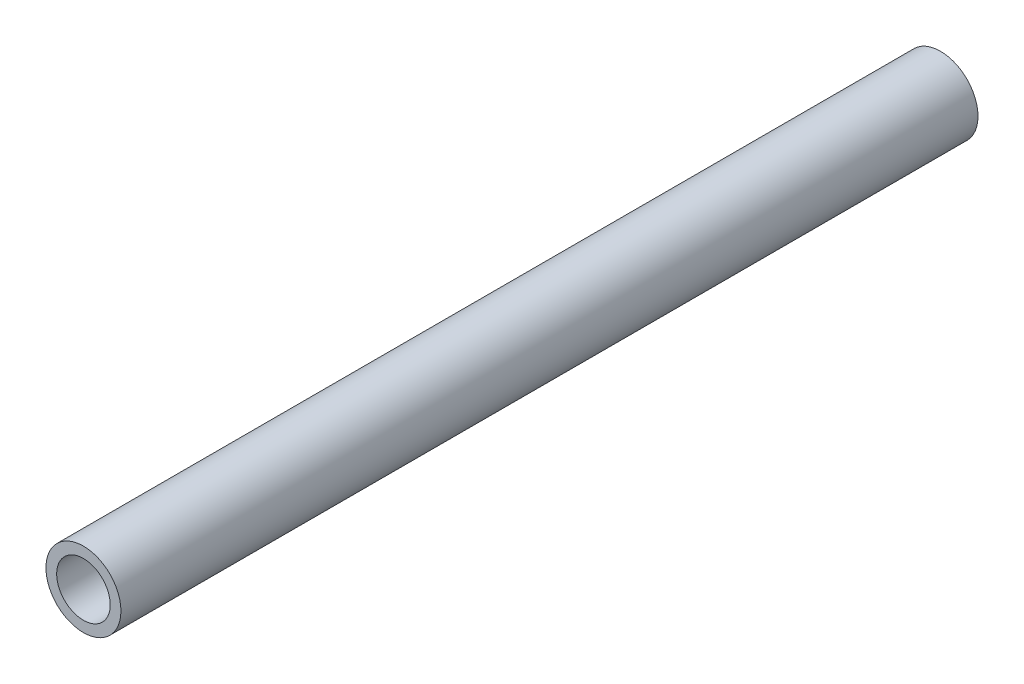
SolidWorks part; units mm, degrees
material "PVC Rigid"
ref_plane "Front Plane" through (0, 0, 0) normal (0, 0, 1) x (1, 0, 0)
ref_plane "Top Plane" through (0, 0, 0) normal (0, 1, 0) x (1, 0, 0)
ref_plane "Right Plane" through (0, 0, 0) normal (1, 0, 0) x (0, 0, -1)
sketch "Sketch1" plane through (0, 0, 0) normal (0, 0, 1) x (1, 0, 0)
  circle A0 centre (0, 0) radius 13.335
  dimension "D1" = 26.67
extrude "Boss-Extrude1" add sketch "Sketch1" along normal blind 304.8
sketch "Sketch2" plane through (0, 0, 0) normal (0, 0, -1) x (-1, 0, 0)
  circle A0 centre (0, 0) radius 9.525
  dimension "D1" = 19.05
extrude "Cut-Extrude1" cut sketch "Sketch2" against normal through all
equation "\"1foot\"=0.1"
